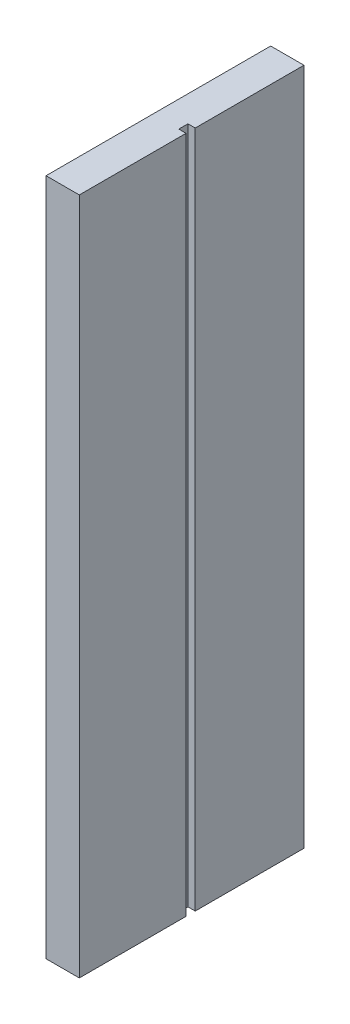
SolidWorks part; units mm, degrees
ref_plane "前视基准面" through (0, 0, 0) normal (0, 0, 1) x (1, 0, 0)
ref_plane "上视基准面" through (0, 0, 0) normal (0, 1, 0) x (1, 0, 0)
ref_plane "右视基准面" through (0, 0, 0) normal (1, 0, 0) x (0, 0, -1)
sketch "草图1" plane through (0, 0, 0) normal (0, 1, 0) x (1, 0, 0)
  line L0 (0, -26.1414) -> (-1.7487, -26.1414)
  line L1 (0, 0) -> (-8, 0)
  line L2 (0, 0) -> (0, -26.1414)
  line L3 (0, -54) -> (-8, -54)
  line L4 (-8, 0) -> (-8, -54)
  line L5 (-1.7487, -26.1414) -> (-1.7487, -28.3424)
  line L6 (-1.7487, -28.3424) -> (0, -28.3424)
  line L7 (0, -28.3424) -> (0, -54)
  dimension "D1" = 8
  dimension "D2" = 54
extrude "凸台-拉伸1" add sketch "草图1" against normal blind 163 contours L1 L4 L3 L7 L6 L5 L0 L2
sketch "草图2" plane through (0, 0, 0) normal (0, 0, -1) x (-1, 0, 0)
  line L0 (8, -163) -> (8, 0) construction
  line L1 (8, -22.9429) -> (3.9152, -22.9429)
  line L2 (8, -22.9429) -> (8, -18.9851)
  line L3 (8, -18.9851) -> (3.9152, -18.9851)
  line L4 (3.9152, -22.9429) -> (3.9152, -18.9851)
extrude "凸台-拉伸2" add sketch "草图2" along normal blind 2
sketch "草图3" plane through (0, 0, 0) normal (0, 0, -1) x (-1, 0, 0)
  line L0 (8, -163) -> (8, -22.9429) construction
  line L1 (8, -91.0881) -> (3.5589, -91.0881)
  line L2 (8, -91.0881) -> (8, -86.9299)
  line L3 (8, -86.9299) -> (3.5589, -86.9299)
  line L4 (3.5589, -91.0881) -> (3.5589, -86.9299)
  line L6 (8, -147.987) -> (3.5589, -147.987)
  line L7 (8, -147.987) -> (8, -143.1198)
  line L8 (8, -143.1198) -> (3.5589, -143.1198)
  line L9 (3.5589, -147.987) -> (3.5589, -143.1198)
extrude "凸台-拉伸3" add sketch "草图3" along normal blind 2 contours L2 L1 L4 L3
sketch "草图4" plane through (0, 0, 0) normal (0, 0, -1) x (-1, 0, 0)
  line L0 (8, -163) -> (8, -91.0881) construction
  line L1 (8, -145.314) -> (3.9492, -145.314)
  line L2 (8, -145.314) -> (8, -140.8659)
  line L3 (8, -140.8659) -> (3.9492, -140.8659)
  line L4 (3.9492, -145.314) -> (3.9492, -140.8659)
  line L6 (119.81, -129.9022) -> (144.2663, -129.9022)
  line L7 (119.81, -129.9022) -> (119.81, -125.1398)
  line L8 (119.81, -125.1398) -> (144.2663, -125.1398)
  line L9 (144.2663, -129.9022) -> (144.2663, -125.1398)
extrude "凸台-拉伸4" add sketch "草图4" along normal blind 2 contours L2 L1 L4 L3
